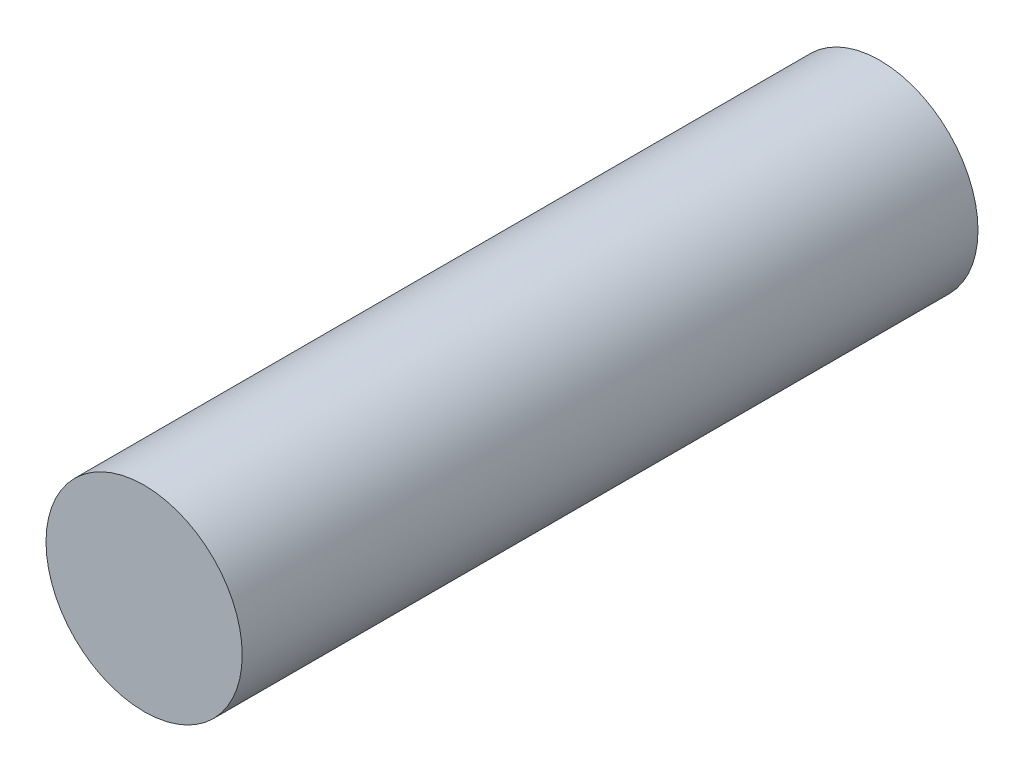
SolidWorks part; units mm, degrees
ref_plane "Alzado" through (0, 0, 0) normal (0, 0, 1) x (1, 0, 0)
ref_plane "Planta" through (0, 0, 0) normal (0, 1, 0) x (1, 0, 0)
ref_plane "Vista lateral" through (0, 0, 0) normal (1, 0, 0) x (0, 0, -1)
sketch "Croquis1" plane through (0, 0, 0) normal (0, 0, 1) x (1, 0, 0)
  circle A0 centre (0, 0) radius 40
  dimension "D1" = 80
extrude "Saliente-Extruir1" add sketch "Croquis1" along normal blind 300
